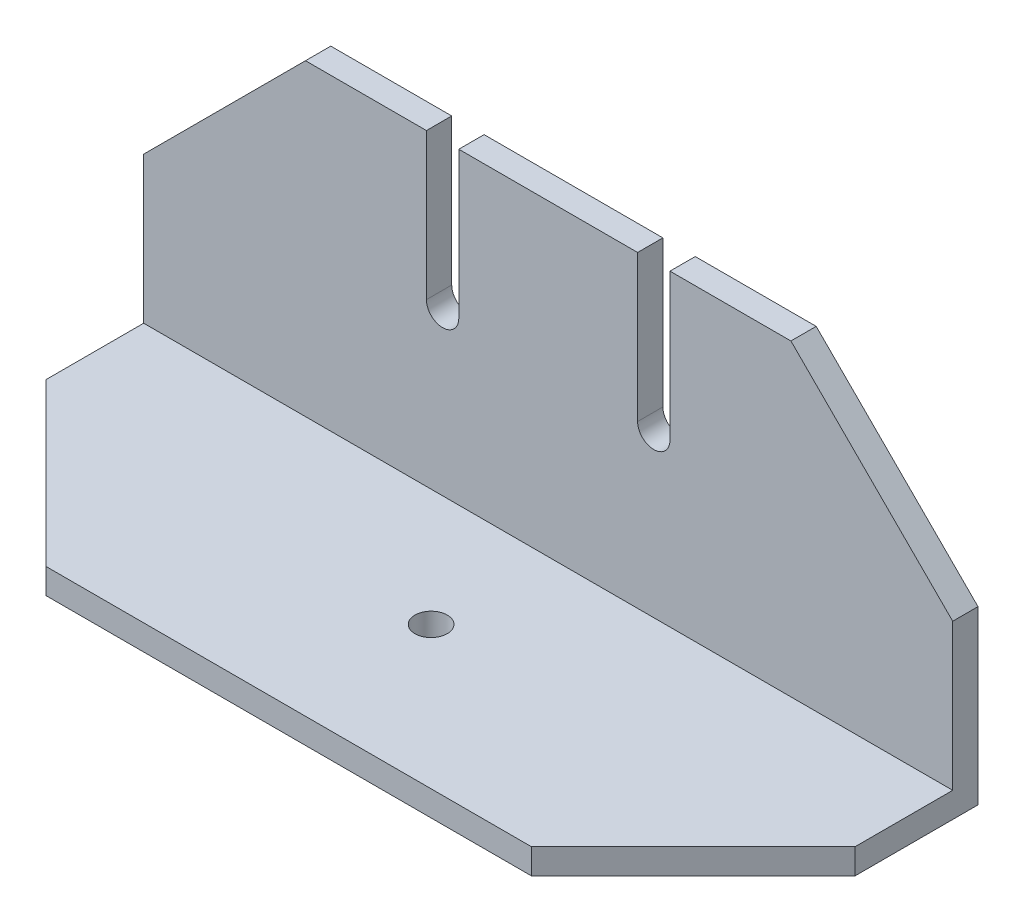
SolidWorks part; units mm, degrees
ref_plane "Front Plane" through (0, 0, 0) normal (0, 0, 1) x (1, 0, 0)
ref_plane "Top Plane" through (0, 0, 0) normal (0, 1, 0) x (1, 0, 0)
ref_plane "Right Plane" through (0, 0, 0) normal (1, 0, 0) x (0, 0, -1)
sketch "Sketch1" plane through (0, 0, 0) normal (1, 0, 0) x (0, 0, -1)
  line L0 (0, 0) -> (32.073, 0)
  line L1 (32.073, 0) -> (32.073, 38.1)
extrude "Extrude-Thin1" add sketch "Sketch1" along normal blind 100 thin
sketch "Sketch2" plane through (0, 0, -35.198) normal (0, 0, -1) x (-1, 0, 0)
  line L0 (-50, 38.1) -> (-50, -3.125) construction
  line L1 (-100, 38.1) -> (0, 38.1) construction
  line L2 (-100, -3.125) -> (0, -3.125) construction
  line L3 (-101.0395, 20) -> (-1.0395, 20) construction
  line L4 (-61.05, 20) -> (-61.05, 38.1)
  line L5 (-61.05, 38.1) -> (-65.05, 38.1)
  line L6 (-65.05, 38.1) -> (-65.05, 20)
  line L7 (-38.95, 20) -> (-38.95, 38.1)
  line L8 (-34.95, 38.1) -> (-34.95, 20)
  line L9 (-38.95, 38.1) -> (-34.95, 38.1)
  arc A0 (-34.95, 20) -> (-38.95, 20) centre (-36.95, 20) cw
  arc A1 (-65.05, 20) -> (-61.05, 20) centre (-63.05, 20) ccw
  dimension "D3" = 13.05
  dimension "D1" = 23.125
extrude "Cut-Extrude1" cut sketch "Sketch2" against normal through all
chamfer "Chamfer1" distance 20 angle 45 2 edges at (100, 38.1, -33.6355) (0, 38.1, -33.6355)
chamfer "Chamfer2" distance 20 angle 45 2 edges at (0, -1.5625, 0) (100, -1.5625, 0)
sketch "Sketch3" plane through (0, -3.125, 0) normal (0, -1, 0) x (1, 0, 0)
  line L0 (50, -35.198) -> (50, 0) construction
  line L1 (100, -35.198) -> (0, -35.198) construction
  line L2 (80, 0) -> (20, 0) construction
  circle A0 centre (50, -17.599) radius 2
extrude "Cut-Extrude2" cut sketch "Sketch3" against normal through all
